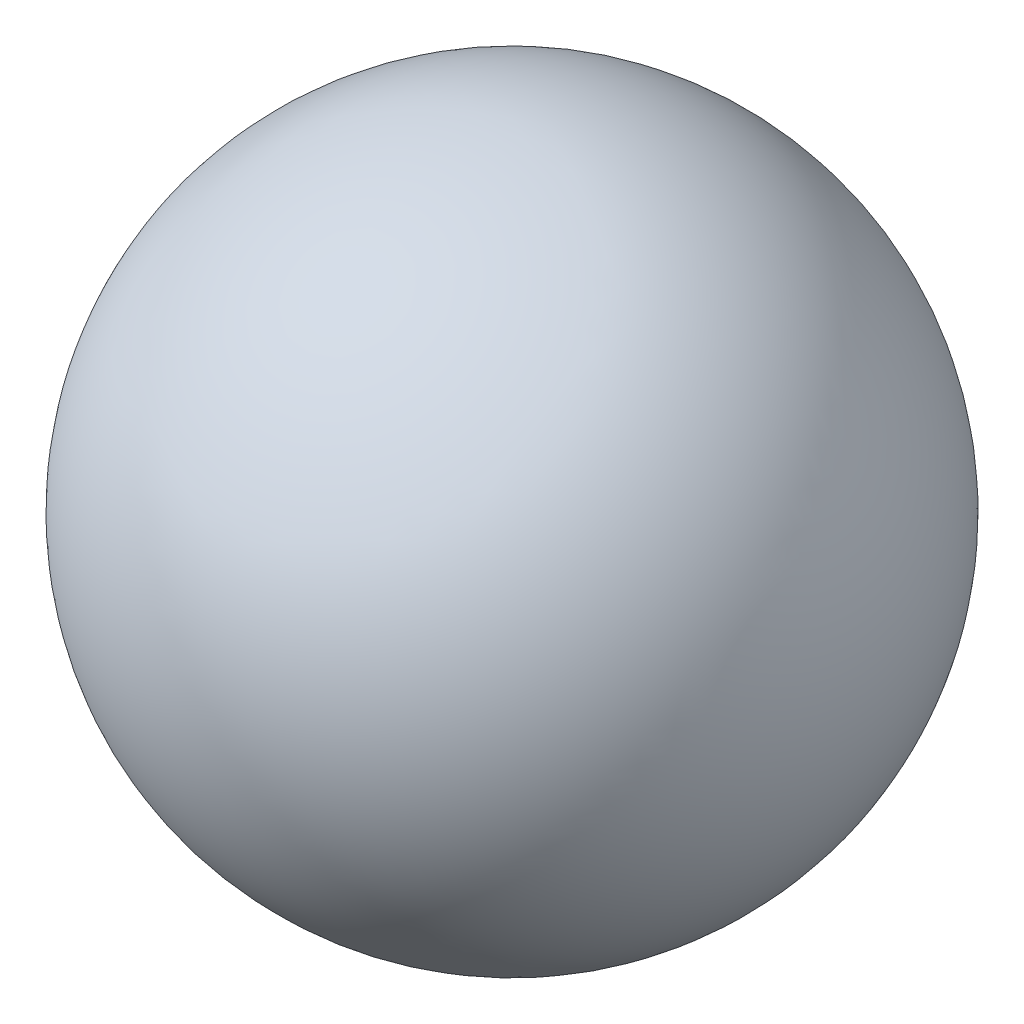
SolidWorks part; units mm, degrees
ref_plane "Front Plane" through (0, 0, 0) normal (0, 0, 1) x (1, 0, 0)
ref_plane "Top Plane" through (0, 0, 0) normal (0, 1, 0) x (1, 0, 0)
ref_plane "Right Plane" through (0, 0, 0) normal (1, 0, 0) x (0, 0, -1)
sketch "Sketch1" plane through (0, 0, 0) normal (0, 1, 0) x (1, 0, 0)
  line L0 (-19.939, 0) -> (19.939, 0)
  arc A1 (19.939, 0) -> (-19.939, 0) centre (0, 0) ccw
  dimension "D1" = 39.878
revolve "Revolve5" add sketch "Sketch1" angle 360 about L0
